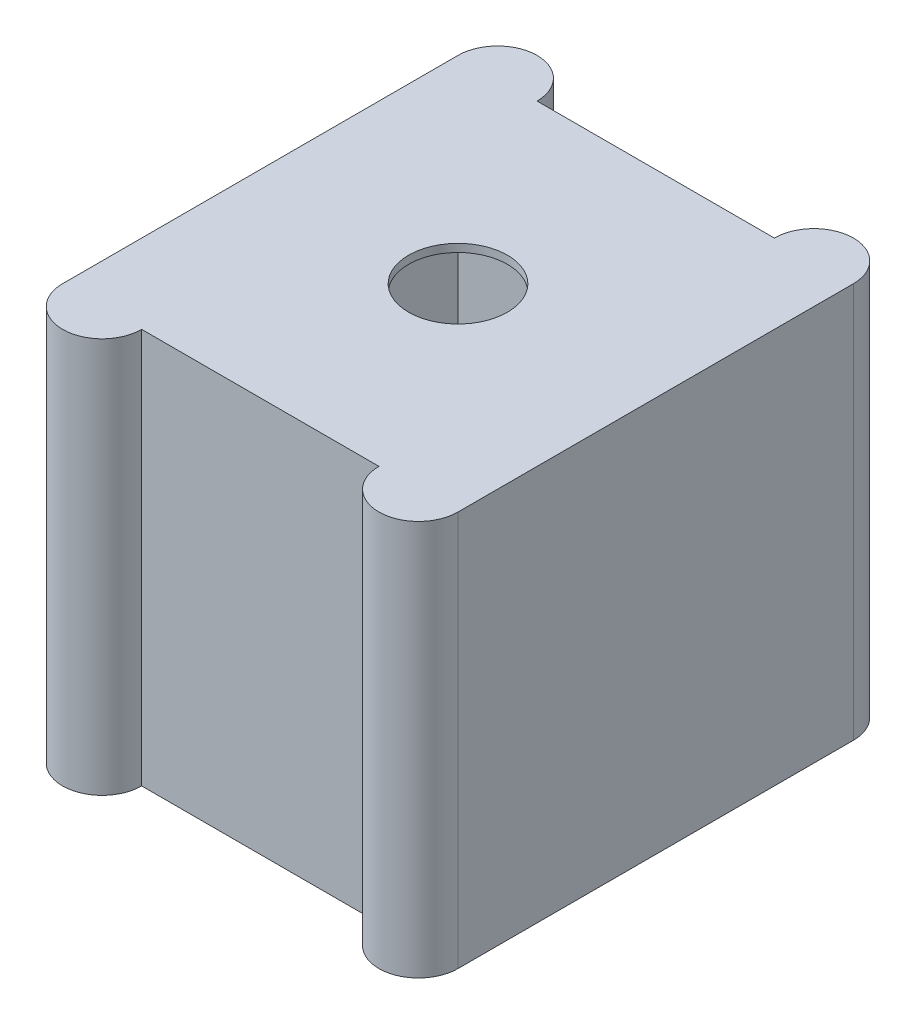
SolidWorks part; units mm, degrees
ref_plane "Front Plane" through (0, 0, 0) normal (0, 0, 1) x (1, 0, 0)
ref_plane "Top Plane" through (0, 0, 0) normal (0, 1, 0) x (1, 0, 0)
ref_plane "Right Plane" through (0, 0, 0) normal (1, 0, 0) x (0, 0, -1)
sketch "Sketch1" plane through (0, 0, 0) normal (0, 1, 0) x (1, 0, 0)
  line L0 (0, 0) -> (0, -164.7719) construction
  line L1 (-30, 50) -> (30, 50)
  line L2 (-50, 50) -> (-50, -50)
  line L3 (-30, -50) -> (30, -50)
  line L4 (50, 50) -> (50, -50)
  line L5 (-50, 50) -> (50, -50) construction
  line L6 (-50, -50) -> (50, 50) construction
  line L7 (0, 0) -> (230.7692, 0) construction
  arc A0 (-50, 50) -> (-30, 50) centre (-40, 50) cw
  arc A1 (50, 50) -> (30, 50) centre (40, 50) ccw
  arc A2 (50, -50) -> (30, -50) centre (40, -50) cw
  arc A3 (-50, -50) -> (-30, -50) centre (-40, -50) ccw
  circle A4 centre (0, 0) radius 12.5
  point P0 (0, 0)
  point P17 (-40, 60)
  dimension "D4" = 25
  dimension "D1" = 100
  dimension "D2" = 100
  dimension "D3" = 10
extrude "Boss-Extrude1" add sketch "Sketch1" along normal blind 100
ref_plane "Plane1" through (0, 98, 0) normal (0, 1, 0) x (1, 0, 0)
sketch "Sketch2" plane through (0, 98, 0) normal (0, 1, 0) x (1, 0, 0)
  line L1 (-48, 48) -> (48, 48)
  line L2 (-48, 48) -> (-48, -48)
  line L3 (-48, -48) -> (48, -48)
  line L4 (48, 48) -> (48, -48)
  line L5 (-48, 48) -> (48, -48) construction
  line L6 (-48, -48) -> (48, 48) construction
  point P0 (0, 0)
  dimension "D1" = 96
  dimension "D2" = 96
extrude "Cut-Extrude1" cut sketch "Sketch2" against normal blind 150
